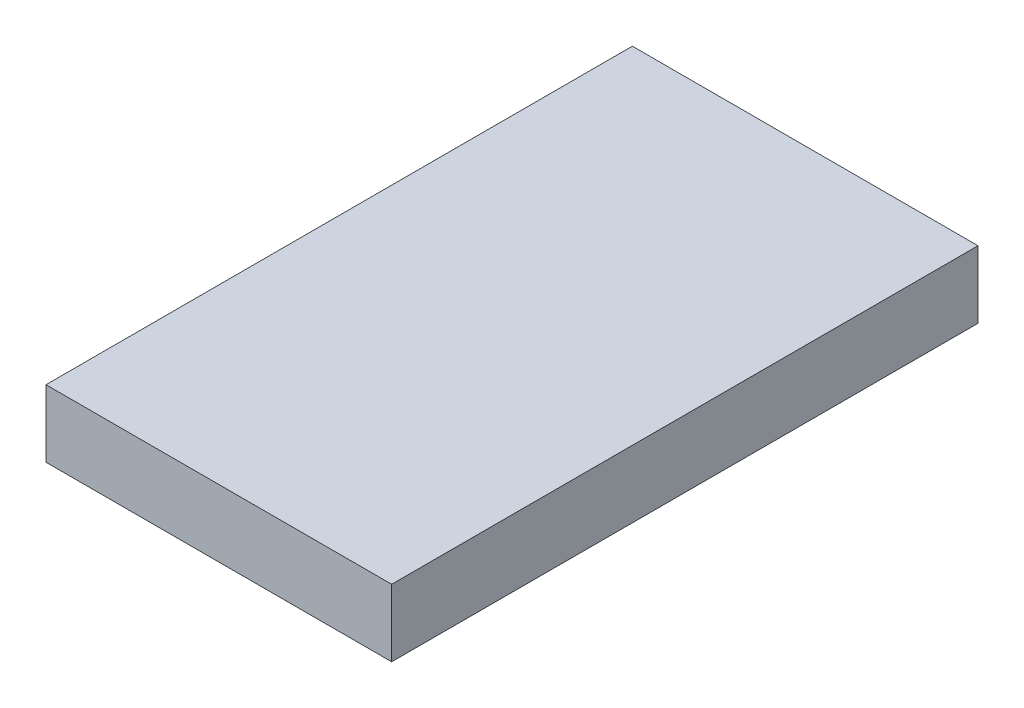
SolidWorks part; units mm, degrees
ref_plane "Front Plane" through (0, 0, 0) normal (0, 0, 1) x (1, 0, 0)
ref_plane "Top Plane" through (0, 0, 0) normal (0, 1, 0) x (1, 0, 0)
ref_plane "Right Plane" through (0, 0, 0) normal (1, 0, 0) x (0, 0, -1)
sketch "Sketch1" plane through (0, 0, 0) normal (0, 1, 0) x (1, 0, 0)
  line L1 (0, 0) -> (24.7, 0)
  line L2 (0, 0) -> (0, 41.9)
  line L3 (0, 41.9) -> (24.7, 41.9)
  line L4 (24.7, 0) -> (24.7, 41.9)
  dimension "D1" = 24.7
  dimension "D2" = 41.9
extrude "Boss-Extrude1" add sketch "Sketch1" along normal blind 4.8 contours L2 L3 L4 L1
